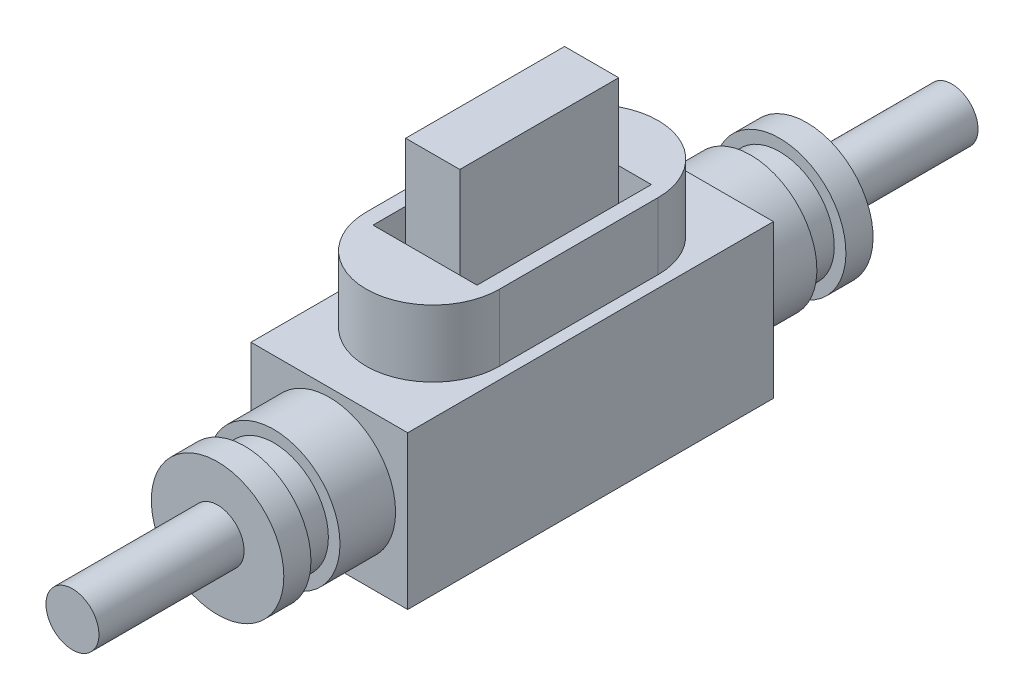
SolidWorks part; units mm, degrees
ref_plane "Front Plane" through (0, 0, 0) normal (0, 0, 1) x (1, 0, 0)
ref_plane "Top Plane" through (0, 0, 0) normal (0, 1, 0) x (1, 0, 0)
ref_plane "Right Plane" through (0, 0, 0) normal (1, 0, 0) x (0, 0, -1)
sketch "Sketch1" plane through (0, 0, 0) normal (0, 1, 0) x (1, 0, 0)
  line L1 (5.4, -12.6) -> (-5.4, -12.6)
  line L2 (5.4, -12.6) -> (5.4, 12.6)
  line L3 (5.4, 12.6) -> (-5.4, 12.6)
  line L4 (-5.4, -12.6) -> (-5.4, 12.6)
  line L5 (5.4, -12.6) -> (-5.4, 12.6) construction
  line L6 (5.4, 12.6) -> (-5.4, -12.6) construction
  point P0 (0, 0)
  dimension "D1" = 10.8
  dimension "D2" = 25.2
extrude "Boss-Extrude1" add sketch "Sketch1" along normal blind 10.55
sketch "Sketch2" plane through (0, 0, 12.6) normal (0, 0, 1) x (1, 0, 0)
  circle A0 centre (0, 5.404) radius 4.565
  dimension "D1" = 9.13
extrude "Boss-Extrude2" add sketch "Sketch2" along normal blind 7.7
sketch "Sketch3" plane through (0, 0, -12.6) normal (0, 0, -1) x (-1, 0, 0)
  circle A0 centre (0, 5.3444) radius 4.565
  dimension "D1" = 9.13
extrude "Boss-Extrude3" add sketch "Sketch3" along normal blind 7.7
sketch "Sketch4" plane through (0, 0, 0) normal (1, 0, 0) x (0, 0, -1)
  line L0 (-20.3, 5.404) -> (-20.3, 0.839)
  line L1 (-12.6, 9.969) -> (-20.3, 9.969) construction
  line L2 (-18.43, 9.969) -> (-18.43, 9.169)
  line L3 (-16.43, 9.169) -> (-18.43, 9.169)
  line L4 (-16.43, 9.169) -> (-16.43, 9.969)
  line L5 (-16.43, 9.969) -> (-18.43, 9.969)
  line L6 (-20.3, 0.839) -> (-20.3, 5.404)
  line L7 (-20.3, 5.404) -> (-12.6, 5.404) construction
  dimension "D1" = 4.565
  dimension "D2" = 2
  dimension "D3" = 0.8
revolve "Cut-Revolve1" cut sketch "Sketch4" angle 360 about L7
sketch "Sketch5" plane through (0, 0, 0) normal (1, 0, 0) x (0, 0, -1)
  line L0 (20.3, 5.3444) -> (20.3, 0.7794)
  line L1 (20.3, 0.7794) -> (20.3, 9.9094) construction
  line L2 (20.3, 5.3444) -> (12.6, 5.3444) construction
  line L5 (20.3, 9.9094) -> (18.43, 9.9094)
  line L6 (20.3, 9.9094) -> (12.6, 9.9094) construction
  line L7 (18.43, 9.9094) -> (18.43, 9.1094)
  line L8 (18.43, 9.1094) -> (16.43, 9.1094)
  line L9 (16.43, 9.1094) -> (16.43, 9.9094)
  line L10 (16.43, 9.9094) -> (18.43, 9.9094)
  dimension "D1" = 4.565
  dimension "D2" = 1.87
  dimension "D3" = 0.8
  dimension "D4" = 2
revolve "Cut-Revolve2" cut sketch "Sketch5" angle 360 about L2
sketch "Sketch6" plane through (0, 10.55, 0) normal (0, 1, 0) x (1, 0, 0)
  line L6 (4.595, -5.465) -> (4.595, 5.465)
  line L8 (-4.595, -5.465) -> (-4.595, 5.465)
  line L9 (4.595, -5.465) -> (-4.595, 5.465) construction
  line L10 (4.595, 5.465) -> (-4.595, -5.465) construction
  arc A2 (-4.595, -5.465) -> (4.595, -5.465) centre (0, -5.465) ccw
  arc A3 (-4.595, 5.465) -> (4.595, 5.465) centre (0, 5.465) cw
  point P0 (0, 0)
  point P1 (0, 0)
  dimension "D2" = 9.19
  dimension "D1" = 10.93
extrude "Boss-Extrude4" add sketch "Sketch6" along normal blind 4.6
sketch "Sketch7" plane through (0, 15.15, 0) normal (0, 1, 0) x (1, 0, 0)
  line L1 (3.585, -6.005) -> (-3.585, -6.005)
  line L2 (3.585, -6.005) -> (3.585, 6.005)
  line L3 (3.585, 6.005) -> (-3.585, 6.005)
  line L4 (-3.585, -6.005) -> (-3.585, 6.005)
  line L5 (3.585, -6.005) -> (-3.585, 6.005) construction
  line L6 (3.585, 6.005) -> (-3.585, -6.005) construction
  point P0 (0, 0)
  dimension "D1" = 12.01
  dimension "D2" = 7.17
extrude "Cut-Extrude1" cut sketch "Sketch7" against normal blind 3.6
sketch "Sketch8" plane through (0, 11.55, 0) normal (0, 1, 0) x (1, 0, 0)
  line L1 (1.865, -5.475) -> (-1.865, -5.475)
  line L2 (1.865, -5.475) -> (1.865, 5.475)
  line L3 (1.865, 5.475) -> (-1.865, 5.475)
  line L4 (-1.865, -5.475) -> (-1.865, 5.475)
  line L5 (1.865, -5.475) -> (-1.865, 5.475) construction
  line L6 (1.865, 5.475) -> (-1.865, -5.475) construction
  point P0 (0, 0)
  dimension "D1" = 3.73
  dimension "D2" = 10.95
extrude "Boss-Extrude5" add sketch "Sketch8" along normal blind 9.38
sketch "Sketch9" plane through (0, 0, -20.3) normal (0, 0, -1) x (-1, 0, 0)
  circle A0 centre (0, 5.4073) radius 1.8
  dimension "D1" = 3.6
extrude "Boss-Extrude6" add sketch "Sketch9" along normal blind 10
sketch "Sketch11" plane through (0, 0, 20.3) normal (0, 0, 1) x (1, 0, 0)
  circle A0 centre (0, 5.5647) radius 1.825
  dimension "D1" = 3.65
extrude "Boss-Extrude7" add sketch "Sketch11" along normal blind 10
